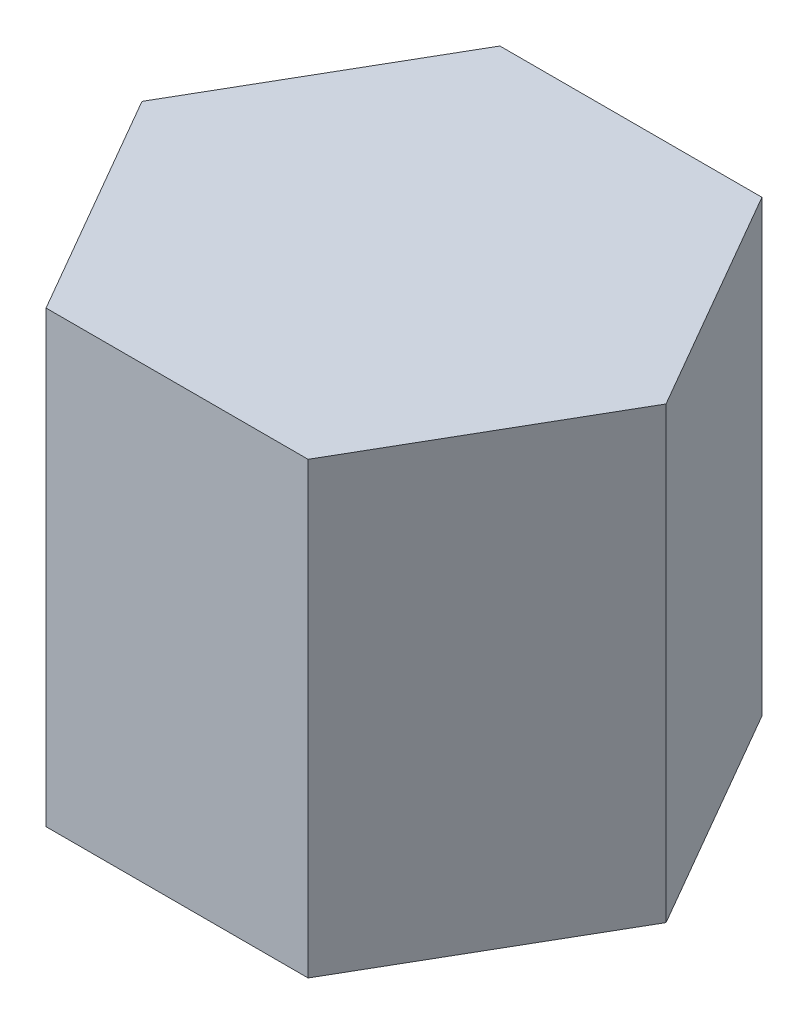
SolidWorks part; units mm, degrees
material "Teak"
ref_plane "Front Plane" through (0, 0, 0) normal (0, 0, 1) x (1, 0, 0)
ref_plane "Top Plane" through (0, 0, 0) normal (0, 1, 0) x (1, 0, 0)
ref_plane "Right Plane" through (0, 0, 0) normal (1, 0, 0) x (0, 0, -1)
sketch "Sketch1" plane through (0, 0, 0) normal (0, 1, 0) x (1, 0, 0)
  line L0 (0, 0) -> (88.9, 0) construction
  line L1 (88.9, 0) -> (44.45, 76.9897)
  line L2 (44.45, 76.9897) -> (-44.45, 76.9897)
  line L3 (-44.45, 76.9897) -> (-88.9, 0)
  line L4 (-88.9, 0) -> (-44.45, -76.9897)
  line L5 (-44.45, -76.9897) -> (44.45, -76.9897)
  line L6 (44.45, -76.9897) -> (88.9, 0)
  circle A0 centre (0, 0) radius 76.9897 construction
  dimension "D1" = 88.9
extrude "Boss-Extrude1" add sketch "Sketch1" along normal blind 152.4
